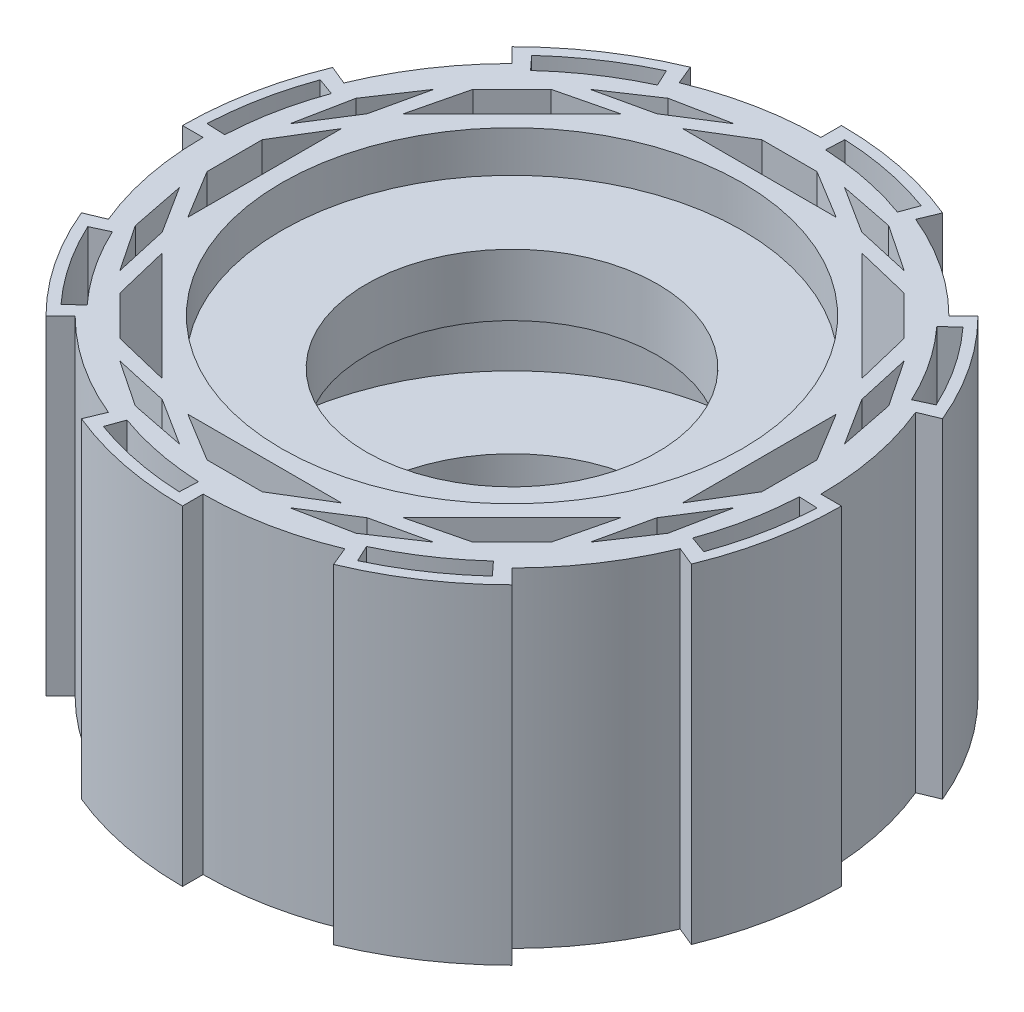
SolidWorks part; units mm, degrees
ref_plane "Front Plane" through (0, 0, 0) normal (0, 0, 1) x (1, 0, 0)
ref_plane "Top Plane" through (0, 0, 0) normal (0, 1, 0) x (1, 0, 0)
ref_plane "Right Plane" through (0, 0, 0) normal (1, 0, 0) x (0, 0, -1)
sketch "Sketch1" plane through (0, 0, 0) normal (0, 1, 0) x (1, 0, 0)
  line L0 (0, -75) -> (0, 75)
  line L1 (-75, 0) -> (75, 0)
  line L5 (28.7013, -69.291) -> (-28.7013, 69.291)
  line L6 (0, 0) -> (28.7013, 69.291)
  line L7 (28.7013, 69.291) -> (-28.7013, -69.291)
  line L9 (-69.291, -28.7013) -> (69.291, 28.7013)
  line L10 (0, 0) -> (-30.6147, 73.9104)
  line L11 (-30.6147, 73.9104) -> (30.6147, -73.9104)
  line L12 (0, -80) -> (0, 80)
  line L13 (0, 0) -> (30.6448, 73.8979)
  line L14 (0, 0) -> (-56.5685, 56.5685)
  line L15 (0, 0) -> (-73.9828, 30.4393)
  line L16 (-73.9828, 30.4393) -> (73.9828, -30.4393)
  line L17 (-28.7013, -69.291) -> (-30.6037, -73.9149)
  line L19 (56.5685, 56.5685) -> (-56.5685, -56.5685)
  line L20 (-69.291, -28.7013) -> (-73.9104, -30.6147)
  line L21 (-73.9104, -30.6147) -> (73.9104, 30.6147)
  line L22 (-80, 0) -> (80, 0)
  line L23 (53.033, -53.033) -> (56.5685, -56.5685)
  circle A0 centre (0, 0) radius 75
  circle A1 centre (0, 0) radius 45
  circle A2 centre (0, 0) radius 80
  dimension "D1" = 150
  dimension "D2" = 90
  dimension "D5" = 160
extrude "Boss-Extrude1" add sketch "Sketch1" along normal blind 80
sketch "Sketch10" plane through (0, 0, 0) normal (0, 1, 0) x (1, 0, 0)
  circle A1 centre (0, 0) radius 60
  circle A3 centre (0, 0) radius 35.3419
  dimension "D1" = 70.6838
  dimension "D2" = 120
extrude "Boss-Extrude6" add sketch "Sketch10" along normal blind 79
sketch "Sketch11" plane through (0, 79, 0) normal (0, 1, 0) x (1, 0, 0)
  circle A0 centre (0, 0) radius 60
extrude "Cut-Extrude6" cut sketch "Sketch11" against normal blind 10
sketch "Sketch12" plane through (0, 0, 0) normal (0, -1, 0) x (1, 0, 0)
  circle A0 centre (0, 0) radius 60
extrude "Cut-Extrude7" cut sketch "Sketch12" against normal blind 55
sketch "Sketch14" plane through (0, 0, 0) normal (0, -1, 0) x (1, 0, 0)
  circle A1 centre (0, 0) radius 60
  circle A2 centre (0, 0) radius 35.3419
  dimension "D1" = 70.6838
extrude "Boss-Extrude7" add sketch "Sketch14" against normal blind 25
sketch "Sketch15" plane through (0, 0, 0) normal (0, -1, 0) x (1, 0, 0)
  circle A0 centre (0, 0) radius 60
extrude "Cut-Extrude8" cut sketch "Sketch15" against normal blind 10
sketch "Sketch25" plane through (0, 80, 0) normal (0, 1, 0) x (1, 0, 0)
  circle A1 centre (0, 0) radius 49
  circle A2 centre (0, 0) radius 58
  dimension "D1" = 98
extrude "Outside Circle Extension 1" add sketch "Sketch25" against normal blind 10
sketch "Sketch26" plane through (0, 0, 0) normal (0, -1, 0) x (1, 0, 0)
  circle A0 centre (0, 0) radius 60
  circle A1 centre (0, 0) radius 49
  dimension "D1" = 98
extrude "Boss-Extrude10" add sketch "Sketch26" against normal blind 10
sketch "Sketch27" plane through (0, 80, 0) normal (0, 1, 0) x (1, 0, 0)
  line L0 (0, 65) -> (0, 70)
  line L1 (0, 70) -> (0, 65)
  line L2 (-70, 0) -> (-65, 0)
  line L3 (45.9619, -45.9619) -> (49.4975, -49.4975)
  line L4 (49.4975, -49.4975) -> (45.9619, -45.9619)
  line L5 (-45.9619, -45.9619) -> (-49.4975, -49.4975)
  line L6 (-49.4975, -49.4975) -> (-45.9619, -45.9619)
  line L7 (26.7878, -64.6716) -> (24.8744, -60.0522)
  line L8 (-64.6716, -26.7878) -> (-60.0522, -24.8744)
  line L9 (24.8744, 60.0522) -> (26.7878, 64.6716)
  line L10 (26.7878, 64.6716) -> (24.8744, 60.0522)
  line L11 (-64.6716, 26.7878) -> (-60.0522, 24.8744)
  line L12 (60.0522, 24.8744) -> (64.6716, 26.7878)
  line L13 (45.9619, 45.9619) -> (49.4975, 49.4975)
  line L14 (-24.8744, -60.0522) -> (-26.7878, -64.6716)
  line L15 (0, -65) -> (0, -70)
  line L16 (-24.8744, 60.0522) -> (-26.7878, 64.6716)
  line L17 (-45.9619, 45.9619) -> (-49.4975, 49.4975)
  line L18 (60.0522, -24.8744) -> (64.6716, -26.7878)
  line L19 (65, 0) -> (70, 0)
  line L20 (-70, 0) -> (-64.6716, 26.7878)
  line L21 (-64.6716, 26.7878) -> (-49.4975, 49.4975)
  line L22 (-49.4975, 49.4975) -> (-26.7878, 64.6716)
  line L23 (-26.7878, 64.6716) -> (0, 70)
  line L24 (0, 70) -> (26.7878, 64.6716)
  line L25 (26.7878, 64.6716) -> (49.4975, 49.4975)
  line L26 (49.4975, 49.4975) -> (64.6716, 26.7878)
  line L27 (70, 0) -> (64.6716, 26.7878)
  line L28 (64.6716, -26.7878) -> (70, 0)
  line L29 (49.4975, -49.4975) -> (64.6716, -26.7878)
  line L30 (26.7878, -64.6716) -> (49.4975, -49.4975)
  line L31 (0, -70) -> (26.7878, -64.6716)
  line L32 (-26.7878, -64.6716) -> (0, -70)
  line L33 (-49.4975, -49.4975) -> (-26.7878, -64.6716)
  line L34 (-49.4975, -49.4975) -> (-64.6716, -26.7878)
  line L35 (-64.6716, -26.7878) -> (-70, 0)
  line L36 (-67.3358, 13.3939) -> (-60.0522, 24.8744)
  line L37 (-67.3358, 13.3939) -> (-65, 0)
  line L38 (-65, 0) -> (-67.3358, -13.3939)
  line L39 (-67.3358, -13.3939) -> (-60.0522, -24.8744)
  line L40 (-60.0522, -24.8744) -> (-57.0845, -38.1427)
  line L41 (-57.0845, -38.1427) -> (-45.9619, -45.9619)
  line L42 (-45.9619, -45.9619) -> (-38.1427, -57.0845)
  line L43 (-38.1427, -57.0845) -> (-24.8744, -60.0522)
  line L44 (-24.8744, -60.0522) -> (-13.3939, -67.3358)
  line L45 (-13.3939, -67.3358) -> (0, -65)
  line L46 (0, -65) -> (13.3939, -67.3358)
  line L47 (13.3939, -67.3358) -> (24.8744, -60.0522)
  line L48 (24.8744, -60.0522) -> (38.1427, -57.0845)
  line L49 (38.1427, -57.0845) -> (45.9619, -45.9619)
  line L50 (45.9619, -45.9619) -> (57.0845, -38.1427)
  line L51 (57.0845, -38.1427) -> (60.0522, -24.8744)
  line L52 (60.0522, -24.8744) -> (67.3358, -13.3939)
  line L53 (67.3358, -13.3939) -> (65, 0)
  line L54 (65, 0) -> (67.3358, 13.3939)
  line L55 (67.3358, 13.3939) -> (60.0522, 24.8744)
  line L56 (60.0522, 24.8744) -> (57.0845, 38.1427)
  line L57 (57.0845, 38.1427) -> (45.9619, 45.9619)
  line L58 (45.2522, 46.6609) -> (38.1427, 57.0845)
  line L59 (38.1427, 57.0845) -> (24.8744, 60.0522)
  line L60 (24.8744, 60.0522) -> (13.3939, 67.3358)
  line L61 (13.3939, 67.3358) -> (0, 65)
  line L62 (0, 65) -> (-13.3939, 67.3358)
  line L63 (-13.3939, 67.3358) -> (-24.8744, 60.0522)
  line L64 (-24.8744, 60.0522) -> (-38.1427, 57.0845)
  line L65 (-38.1427, 57.0845) -> (-45.9619, 45.9619)
  line L66 (-45.9619, 45.9619) -> (-57.0845, 38.1427)
  line L67 (-57.0845, 38.1427) -> (-60.0522, 24.8744)
  circle A0 centre (0, 0) radius 70
  circle A1 centre (0, 0) radius 65
  dimension "D1" = 22.5
extrude "Cut-Extrude14" cut sketch "Sketch27" against normal blind 112 contours L44 L14 L32 | L43 L33 L14 | L40 L8 L34 | L39 L35 L8 | L67 L21 L11 | L20 L36 L11 | L64 L16 L22 | L63 L23 L16 | L60 L9 L24 | L59 L25 L9 | L56 L12 L26 | L55 L27 L12 | L51 L29 L18 | L52 L18 L28 | L48 L7 L30 | L47 L31 L7
sketch "Sketch28" plane through (0, 80, 0) normal (0, 1, 0) x (1, 0, 0)
  line L0 (-24.8744, 60.0522) -> (24.8744, 60.0522)
  line L1 (24.8744, 60.0522) -> (60.0522, 24.8744)
  line L2 (60.0522, 24.8744) -> (60.0522, -24.8744)
  line L3 (60.0522, -24.8744) -> (24.8744, -60.0522)
  line L4 (24.8744, -60.0522) -> (38.1427, -57.0845) construction
  line L5 (24.8744, -60.0522) -> (-24.8744, -60.0522)
  line L6 (-24.8744, -60.0522) -> (-60.0522, -24.8744)
  line L7 (-60.0522, -24.8744) -> (-60.0522, 24.8744)
  line L8 (-60.0522, 24.8744) -> (-24.8744, 60.0522)
  line L9 (-57.0845, 38.1427) -> (-38.1427, 57.0845)
  line L10 (-60.0522, 24.8744) -> (-42.4633, 42.4633)
  line L11 (-47.6136, 47.6136) -> (-51.2577, 33.6689)
  line L12 (-42.4633, 42.4633) -> (-24.8744, 60.0522)
  line L13 (-33.6689, 51.2577) -> (-47.6136, 47.6136)
  line L14 (-60.0522, 24.8744) -> (-51.2577, 33.6689)
  line L15 (-57.0845, 38.1427) -> (-47.6136, 47.6136)
  line L16 (-55.655, 29.2716) -> (-52.3491, 42.8781)
  line L17 (-38.1427, 57.0845) -> (-24.8744, 60.0522)
  line L18 (-33.6689, 51.2577) -> (-24.8744, 60.0522)
  line L19 (-47.6136, 47.6136) -> (-38.1427, 57.0845)
  line L20 (-29.2716, 55.655) -> (-42.8781, 52.3491)
  line L21 (-24.8744, 60.0522) -> (0, 60.0522)
  line L22 (0, 60.0522) -> (24.8744, 60.0522)
  line L23 (-13.3939, 67.3358) -> (13.3939, 67.3358)
  line L24 (-24.8744, 60.0522) -> (0, 60.0522)
  line L25 (-12.4372, 60.0522) -> (0, 67.3358)
  line L26 (24.8744, 60.0522) -> (0, 60.0522)
  line L27 (12.4372, 60.0522) -> (0, 67.3358)
  line L28 (-24.8744, 60.0522) -> (-12.4372, 60.0522)
  line L29 (-13.3939, 67.3358) -> (0, 67.3358)
  line L30 (0, 67.3358) -> (13.3939, 67.3358)
  line L31 (24.8744, 60.0522) -> (12.4372, 60.0522)
  line L32 (-18.6558, 60.0522) -> (-6.697, 67.3358)
  line L33 (24.8744, 60.0522) -> (12.4372, 60.0522)
  line L34 (0, 67.3358) -> (13.3939, 67.3358)
  line L35 (6.697, 67.3358) -> (18.6558, 60.0522)
  line L36 (38.1427, 57.0845) -> (57.0845, 38.1427)
  line L37 (57.0845, 38.1427) -> (47.6136, 47.6136)
  line L38 (47.6136, 47.6136) -> (38.1427, 57.0845)
  line L39 (24.8744, 60.0522) -> (42.4633, 42.4633)
  line L40 (42.4633, 42.4633) -> (60.0522, 24.8744)
  line L41 (51.2577, 33.6689) -> (47.6136, 47.6136)
  line L42 (33.6689, 51.2577) -> (47.6136, 47.6136)
  line L43 (38.1427, 57.0845) -> (47.6136, 47.6136)
  line L44 (24.8744, 60.0522) -> (33.6689, 51.2577)
  line L45 (29.2716, 55.655) -> (42.8781, 52.3491)
  line L46 (47.6136, 47.6136) -> (57.0845, 38.1427)
  line L47 (51.2577, 33.6689) -> (60.0522, 24.8744)
  line L48 (55.655, 29.2716) -> (52.3491, 42.8781)
  line L49 (67.3358, 13.3939) -> (67.3358, -13.3939)
  line L50 (67.3358, -13.3939) -> (67.3358, 0)
  line L51 (67.3358, 0) -> (67.3358, 13.3939)
  line L52 (60.0522, 24.8744) -> (60.0522, 0)
  line L53 (60.0522, 0) -> (60.0522, -24.8744)
  line L54 (60.0522, -12.4372) -> (67.3358, 0)
  line L55 (60.0522, 12.4372) -> (67.3358, 0)
  line L56 (60.0522, 24.8744) -> (60.0522, 12.4372)
  line L57 (67.3358, 0) -> (67.3358, 13.3939)
  line L58 (67.3358, 0) -> (67.3358, -13.3939)
  line L59 (60.0522, -24.8744) -> (60.0522, -12.4372)
  line L60 (60.0522, 18.6558) -> (67.3358, 6.697)
  line L61 (60.0522, -24.8744) -> (60.0522, -12.4372)
  line L62 (67.3358, 0) -> (67.3358, -13.3939)
  line L63 (67.3358, 0) -> (67.3358, -13.3939)
  line L64 (67.3358, -6.697) -> (60.0522, -18.6718)
  line L65 (60.0522, -24.8744) -> (42.4633, -42.4633)
  line L66 (42.4633, -42.4633) -> (24.8744, -60.0522)
  line L67 (57.0845, -38.1427) -> (38.1427, -57.0845)
  line L68 (60.0522, -24.8744) -> (42.4633, -42.4633)
  line L69 (60.0522, -24.8744) -> (42.4633, -42.4633)
  line L70 (42.4633, -42.4633) -> (24.8744, -60.0522)
  line L71 (51.2577, -33.6689) -> (47.6136, -47.6136)
  line L72 (47.6136, -47.6136) -> (33.6689, -51.2577)
  line L73 (33.6689, -51.2577) -> (24.8744, -60.0522)
  line L74 (57.0845, -38.1427) -> (47.6136, -47.6136)
  line L75 (38.1427, -57.0845) -> (47.6136, -47.6136)
  line L76 (60.0522, -24.8744) -> (51.2577, -33.6689)
  line L77 (55.655, -29.2716) -> (52.3491, -42.8781)
  line L78 (52.3491, -42.8781) -> (42.8781, -52.3491)
  line L79 (42.8781, -52.3491) -> (29.2716, -55.655)
  line L80 (13.3939, -67.3358) -> (-13.3939, -67.3358)
  line L81 (-13.3939, -67.3358) -> (0, -67.3358)
  line L82 (0, -67.3358) -> (13.3939, -67.3358)
  line L83 (24.8744, -60.0522) -> (0, -60.0522)
  line L84 (0, -60.0522) -> (-24.8744, -60.0522)
  line L85 (12.4372, -60.0522) -> (0, -67.3358)
  line L86 (-12.4372, -60.0522) -> (0, -67.3358)
  line L87 (24.8744, -60.0522) -> (12.4372, -60.0522)
  line L88 (13.3939, -67.3358) -> (0, -67.3358)
  line L89 (0, -67.3358) -> (-13.3939, -67.3358)
  line L90 (-24.8744, -60.0522) -> (-12.4372, -60.0522)
  line L91 (18.6558, -60.0522) -> (6.697, -67.3358)
  line L92 (6.697, -67.3358) -> (-6.697, -67.3358)
  line L93 (-6.697, -67.3358) -> (-18.6558, -60.0522)
  line L94 (-38.1427, -57.0845) -> (-57.0845, -38.1427)
  line L95 (-57.0845, -38.1427) -> (-47.6136, -47.6136)
  line L96 (-42.4633, -42.4633) -> (-24.8744, -60.0522)
  line L97 (-42.4633, -42.4633) -> (-60.0522, -24.8744)
  line L98 (-51.2577, -33.6689) -> (-47.6136, -47.6136)
  line L99 (-33.6689, -51.2577) -> (-47.6136, -47.6136)
  line L100 (-24.8744, -60.0522) -> (-33.6689, -51.2577)
  line L101 (-38.1427, -57.0845) -> (-47.6136, -47.6136)
  line L102 (-47.6136, -47.6136) -> (-57.0845, -38.1427)
  line L103 (-51.2577, -33.6689) -> (-60.0522, -24.8744)
  line L104 (-29.2716, -55.655) -> (-42.8781, -52.3491)
  line L105 (-42.8781, -52.3491) -> (-52.3491, -42.8781)
  line L106 (-52.3491, -42.8781) -> (-55.655, -29.2716)
  line L107 (-67.3358, -13.3939) -> (-67.3358, 13.3939)
  line L108 (-60.0522, -24.8744) -> (-60.0522, 0)
  line L109 (-60.0522, 0) -> (-60.0522, 24.8744)
  line L110 (-60.0522, -12.4372) -> (-67.3358, 0)
  line L111 (-60.0522, 0) -> (-60.0522, 24.8744)
  line L112 (-60.0522, 12.4372) -> (-67.3358, 0)
  line L113 (-60.0522, -24.8744) -> (-60.0522, -12.4372)
  line L114 (-67.3358, -13.3939) -> (-67.3358, 0)
  line L115 (-67.3358, 0) -> (-67.3358, 13.3939)
  line L116 (-60.0522, 12.4372) -> (-60.0522, 24.8744)
  line L117 (-60.0522, 18.6558) -> (-67.3358, 6.697)
  line L118 (-67.3358, -13.3939) -> (-67.3358, 0)
  line L119 (-60.0522, -24.8744) -> (-60.0522, -12.4372)
  line L120 (-60.0522, -18.6558) -> (-67.3358, -6.697)
  circle A0 centre (0, 0) radius 60.0522
  point P70 (60.0522, -18.6718)
extrude "Cut-Extrude17" cut sketch "Sketch28" against normal blind 112 contours L120 L119 L110 L118 | L7 L112 L110 L108 | L111 L117 L107 L112 | L16 L14 L11 L15 | L8 L13 L11 L10 | L12 L20 L9 L13 | L32 L28 L25 L29 | L0 L27 L25 L24 | L35 L23 L27 L26 | L45 L44 L42 L43 | L42 L39 L1 L41 | L40 L48 L36 L41 | L60 L56 L55 L57 | L55 L52 L2 L54 | L64 L49 L54 L53 | L77 L76 L71 L74 | L72 L71 L69 L3 | L79 L67 L72 L70 | L91 L87 L85 L88 | L5 L86 L85 L83 | L93 L80 L86 L84 | L104 L100 L99 L101 | L99 L96 L6 L98 | L106 L94 L98 L97
sketch "Sketch29" plane through (0, 25, 0) normal (0, 1, 0) x (1, 0, 0)
  circle A0 centre (0, 0) radius 60
  circle A1 centre (0, 0) radius 35.3419
extrude "Boss-Extrude11" add sketch "Sketch29" along normal blind 1
sketch "Sketch30" plane through (0, 55, 0) normal (0, -1, 0) x (1, 0, 0)
  circle A0 centre (0, 0) radius 35.3419
  circle A1 centre (0, 0) radius 60
extrude "Boss-Extrude12" add sketch "Sketch30" along normal blind 1
sketch "Sketch31" plane through (0, 80, 0) normal (0, 1, 0) x (1, 0, 0)
  circle A0 centre (0, 0) radius 55.9147
  dimension "D1" = 111.8295
extrude "Cut-Extrude18" cut sketch "Sketch31" against normal blind 10
sketch "Sketch32" plane through (0, 0, 0) normal (0, -1, 0) x (1, 0, 0)
  circle A0 centre (0, 0) radius 55.9147
  dimension "D1" = 111.8295
extrude "Cut-Extrude19" cut sketch "Sketch32" against normal blind 10
sketch "Sketch34" plane through (0, 80, 0) normal (0, 1, 0) x (1, 0, 0)
  line L0 (-77.4262, 3.3805) -> (-72.9305, 3.1842)
  line L6 (-72.8888, 26.3338) -> (-68.6566, 24.8047)
  line L8 (-52.3582, 57.139) -> (-49.3181, 53.8212)
  line L11 (-32.7529, 70.2389) -> (-30.8511, 66.1605)
  line L12 (3.1842, 72.9305) -> (3.3805, 77.4262)
  line L16 (24.9955, 68.5874) -> (26.5363, 72.8154)
  line L19 (57.139, 52.3582) -> (53.8212, 49.3181)
  line L22 (66.1605, 30.8511) -> (70.2389, 32.7529)
  line L25 (75, 0) -> (77.5, 0)
  line L27 (72.8888, -26.3338) -> (68.6566, -24.8047)
  line L28 (77.4262, -3.3805) -> (72.9305, -3.1842)
  line L30 (-27.9359, 67.4432) -> (27.9359, -67.4432)
  line L34 (32.7529, -70.2389) -> (30.8511, -66.1605)
  line L35 (52.3582, -57.139) -> (49.3181, -53.8212)
  line L39 (-26.3338, -72.8888) -> (-24.8047, -68.6566)
  line L40 (-3.3805, -77.4262) -> (-3.1842, -72.9305)
  line L41 (-57.139, -52.3582) -> (-53.8212, -49.3181)
  line L42 (-70.2389, -32.7529) -> (-66.1605, -30.8511)
  circle A5 centre (0, 0) radius 73
  arc A6 (-72.8888, 26.3338) -> (-77.4262, 3.3805) centre (0, 0) ccw
  arc A7 (-26.3338, -72.8888) -> (-3.3805, -77.4262) centre (0, 0) ccw
  arc A9 (-70.2389, -32.7529) -> (-57.139, -52.3582) centre (0, 0) ccw
  arc A10 (-72.8888, 26.3338) -> (-77.4262, 3.3805) centre (0, 0) ccw
  arc A11 (-32.7529, 70.2389) -> (-52.3582, 57.139) centre (0, 0) ccw
  arc A12 (26.5363, 72.8154) -> (3.3805, 77.4262) centre (0, 0) ccw
  arc A13 (70.2389, 32.7529) -> (57.139, 52.3582) centre (0, 0) ccw
  arc A14 (72.8888, -26.3338) -> (77.4262, -3.3805) centre (0, 0) ccw
  arc A15 (32.7529, -70.2389) -> (52.3582, -57.139) centre (0, 0) ccw
  dimension "D8" = 2.5
  dimension "D9" = 2.5
extrude "Cut-Extrude20" cut sketch "Sketch34" against normal blind 216 and the other way blind 66 contours L11 A11 L8 A5 | L16 A12 L12 A5 | L22 A13 L19 A5 | L27 A14 L28 A5 | L34 A15 L35 A5 | L39 A7 L40 A5 | L42 A9 L41 A5 | L6 A6 L0 A5
